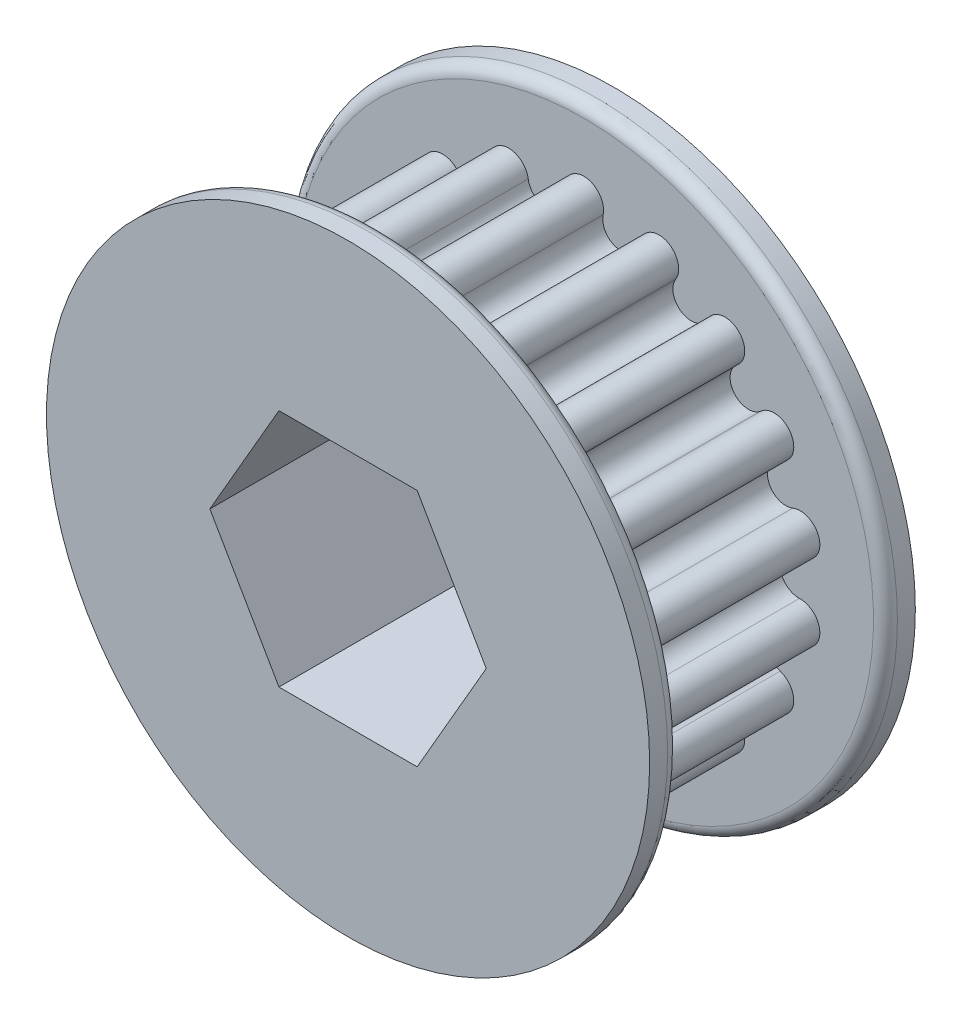
SolidWorks part; units mm, degrees
ref_plane "Front Plane" through (0, 0, 0) normal (0, 0, 1) x (1, 0, 0)
ref_plane "Top Plane" through (0, 0, 0) normal (0, 1, 0) x (1, 0, 0)
ref_plane "Right Plane" through (0, 0, 0) normal (1, 0, 0) x (0, 0, -1)
sketch "Sketch1" plane through (0, 0, 0) normal (0, 0, 1) x (1, 0, 0)
  line L1 (7.3323, 0) -> (3.6662, 6.35)
  line L2 (3.6662, 6.35) -> (-3.6662, 6.35)
  line L3 (-3.6662, 6.35) -> (-7.3323, 0)
  line L4 (-7.3323, 0) -> (-3.6662, -6.35)
  line L5 (-3.6662, -6.35) -> (3.6662, -6.35)
  line L6 (3.6662, -6.35) -> (7.3323, 0)
  circle A0 centre (0, 0) radius 6.35 construction
  arc A1 (1.023, 11.4384) -> (-1.023, 11.4384) centre (0, 11.6544) ccw
  arc A2 (4.8735, 10.3986) -> (2.9508, 11.0984) centre (3.986, 10.9516) ccw
  arc A3 (4.8735, 10.3986) -> (6.5688, 9.4199) centre (5.7047, 9.8808) ccw
  arc A4 (8.1361, 8.1047) -> (6.5688, 9.4199) centre (7.4913, 8.9278) ccw
  arc A5 (8.1361, 8.1047) -> (9.3944, 6.6051) centre (8.74, 7.3338) ccw
  arc A6 (10.4174, 4.8332) -> (9.3944, 6.6051) centre (10.093, 5.8272) ccw
  arc A7 (10.4174, 4.8332) -> (11.0869, 2.9937) centre (10.7212, 3.9022) ccw
  arc A8 (11.4422, 0.9788) -> (11.0869, 2.9937) centre (11.4774, 2.0238) ccw
  arc A9 (11.4422, 0.9788) -> (11.4422, -0.9788) centre (11.4093, 0) ccw
  arc A10 (11.0869, -2.9937) -> (11.4422, -0.9788) centre (11.4774, -2.0238) ccw
  arc A11 (11.0869, -2.9937) -> (10.4174, -4.8332) centre (10.7212, -3.9022) ccw
  arc A12 (9.3944, -6.6051) -> (10.4174, -4.8332) centre (10.093, -5.8272) ccw
  arc A13 (9.3944, -6.6051) -> (8.1361, -8.1047) centre (8.74, -7.3338) ccw
  arc A14 (6.5688, -9.4199) -> (8.1361, -8.1047) centre (7.4913, -8.9278) ccw
  arc A15 (6.5688, -9.4199) -> (4.8735, -10.3986) centre (5.7047, -9.8808) ccw
  arc A16 (2.9508, -11.0984) -> (4.8735, -10.3986) centre (3.986, -10.9516) ccw
  arc A17 (2.9508, -11.0984) -> (1.023, -11.4384) centre (1.9812, -11.236) ccw
  arc A18 (-1.023, -11.4384) -> (1.023, -11.4384) centre (0, -11.6544) ccw
  arc A19 (1.023, 11.4384) -> (2.9508, 11.0984) centre (1.9812, 11.236) ccw
  arc A20 (-1.023, -11.4384) -> (-2.9508, -11.0984) centre (-1.9812, -11.236) ccw
  arc A21 (-4.8735, -10.3986) -> (-2.9508, -11.0984) centre (-3.986, -10.9516) ccw
  arc A22 (-4.8735, -10.3986) -> (-6.5688, -9.4199) centre (-5.7047, -9.8808) ccw
  arc A23 (-8.1361, -8.1047) -> (-6.5688, -9.4199) centre (-7.4913, -8.9278) ccw
  arc A24 (-8.1361, -8.1047) -> (-9.3944, -6.6051) centre (-8.74, -7.3338) ccw
  arc A25 (-10.4174, -4.8332) -> (-9.3944, -6.6051) centre (-10.093, -5.8272) ccw
  arc A26 (-10.4174, -4.8332) -> (-11.0869, -2.9937) centre (-10.7212, -3.9022) ccw
  arc A27 (-11.4422, -0.9788) -> (-11.0869, -2.9937) centre (-11.4774, -2.0238) ccw
  arc A28 (-11.4422, -0.9788) -> (-11.4422, 0.9788) centre (-11.4093, 0) ccw
  arc A29 (-11.0869, 2.9937) -> (-11.4422, 0.9788) centre (-11.4774, 2.0238) ccw
  arc A30 (-11.0869, 2.9937) -> (-10.4174, 4.8332) centre (-10.7212, 3.9022) ccw
  arc A31 (-9.3944, 6.6051) -> (-10.4174, 4.8332) centre (-10.093, 5.8272) ccw
  arc A32 (-9.3944, 6.6051) -> (-8.1361, 8.1047) centre (-8.74, 7.3338) ccw
  arc A33 (-6.5688, 9.4199) -> (-8.1361, 8.1047) centre (-7.4913, 8.9278) ccw
  arc A34 (-6.5688, 9.4199) -> (-4.8735, 10.3986) centre (-5.7047, 9.8808) ccw
  arc A35 (-2.9508, 11.0984) -> (-4.8735, 10.3986) centre (-3.986, 10.9516) ccw
  arc A36 (-2.9508, 11.0984) -> (-1.023, 11.4384) centre (-1.9812, 11.236) ccw
  point P95 (0, 0)
  dimension "D1" = 12.7
extrude "Boss-Extrude1" add sketch "Sketch1" along normal blind 10.922
ref_plane "Plane1" through (0, 0, 5.461) normal (0, 0, 1) x (1, 0, 0)
sketch "Sketch2" plane through (0, 0, 10.922) normal (0, 0, 1) x (1, 0, 0)
  line L0 (-3.6662, 6.35) -> (-7.3323, 0) construction
  line L1 (-7.3323, 0) -> (-3.6662, -6.35) construction
  line L2 (-3.6662, -6.35) -> (3.6662, -6.35) construction
  line L3 (3.6662, -6.35) -> (7.3323, 0) construction
  line L4 (7.3323, 0) -> (3.6662, 6.35) construction
  line L5 (3.6662, 6.35) -> (-3.6662, 6.35) construction
  line L6 (-3.6662, 6.35) -> (-7.3323, 0)
  line L7 (-7.3323, 0) -> (-3.6662, -6.35)
  line L8 (-3.6662, -6.35) -> (3.6662, -6.35)
  line L9 (3.6662, -6.35) -> (7.3323, 0)
  line L10 (7.3323, 0) -> (3.6662, 6.35)
  line L11 (3.6662, 6.35) -> (-3.6662, 6.35)
  circle A0 centre (0, 0) radius 16.002
  dimension "D1" = 32.004
extrude "Boss-Extrude2" add sketch "Sketch2" along normal blind 1.5875
fillet "Fillet1" radius 0.635 1 edges at (16.002, 0, 10.922)
mirror "Mirror1" about plane through (0, 0, 5.461) normal (0, 0, 1) of "Fillet1", "Boss-Extrude2"
